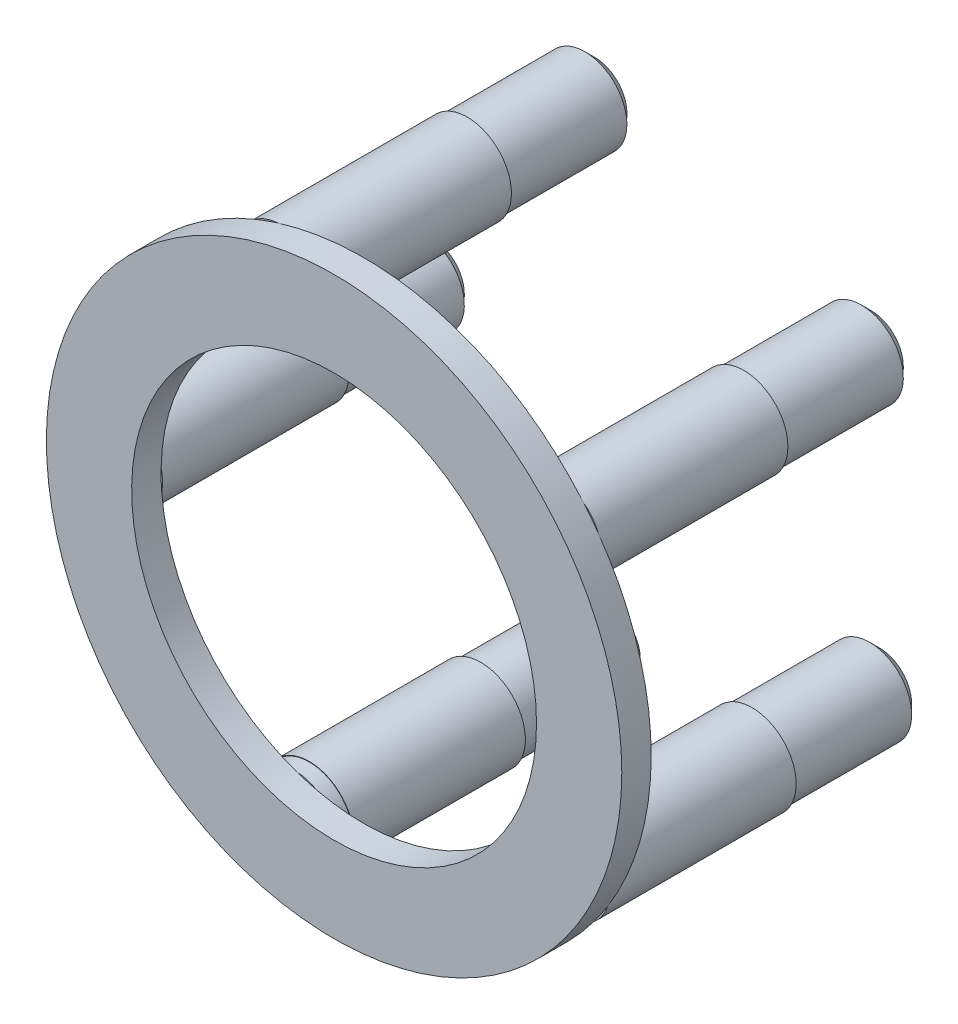
SolidWorks part; units mm, degrees
ref_plane "Front Plane" through (0, 0, 0) normal (0, 0, 1) x (1, 0, 0)
ref_plane "Top Plane" through (0, 0, 0) normal (0, 1, 0) x (1, 0, 0)
ref_plane "Right Plane" through (0, 0, 0) normal (1, 0, 0) x (0, 0, -1)
sketch "Sketch2" plane through (0, 0, -6.0136) normal (0, 0, -1) x (-1, 0, 0)
  circle A0 centre (-20.1422, -37.1244) radius 25 construction
  circle A1 centre (-11.7347, -13.5805) radius 4.5
  circle A2 centre (4.8475, -37.8449) radius 4.5
  circle A3 centre (-13.1052, -61.1136) radius 4.5
  circle A4 centre (-40.7827, -51.2301) radius 4.5
  circle A5 centre (-39.9357, -21.853) radius 4.5
  dimension "D1" = 50
  dimension "D2" = 9
  dimension "D3" = 5
extrude "Boss-Extrude1" add sketch "Sketch2" along normal offset from surface (30 mm away) 11
sketch "Sketch3" plane through (0, 0, -6.0136) normal (0, 0, 1) x (1, 0, 0)
  circle A0 centre (20.1422, -37.1244) radius 29.35
  circle A1 centre (20.1422, -37.1244) radius 20.65
extrude "Boss-Extrude2" add sketch "Sketch3" along normal blind 3
sketch "Sketch4" plane through (0, 0, -36.0136) normal (0, 0, -1) x (-1, 0, 0)
  circle A0 centre (4.8475, -37.8449) radius 4.5
  circle A1 centre (-11.7347, -13.5805) radius 4.5
  circle A2 centre (-39.9357, -21.853) radius 4.5
  circle A3 centre (-40.7827, -51.2301) radius 4.5
  circle A4 centre (-13.1052, -61.1136) radius 4.5
  circle A5 centre (-40.7827, -51.2301) radius 4.5 construction
extrude "Boss-Extrude3" add sketch "Sketch4" along normal blind 2
sketch "Sketch5" plane through (0, 0, -38.0136) normal (0, 0, -1) x (-1, 0, 0)
  circle A0 centre (-13.1052, -61.1136) radius 4.275
  circle A1 centre (-13.1052, -61.1136) radius 4.5
  circle A2 centre (-40.7827, -51.2301) radius 4.275
  circle A3 centre (-40.7827, -51.2301) radius 4.5
  circle A4 centre (-39.9357, -21.853) radius 4.275
  circle A5 centre (-39.9357, -21.853) radius 4.5
  circle A6 centre (-11.7347, -13.5805) radius 4.275
  circle A7 centre (-11.7347, -13.5805) radius 4.5
  circle A8 centre (4.8475, -37.8449) radius 4.275
  circle A9 centre (4.8475, -37.8449) radius 4.5
  point P19 (-20.1422, -37.1244)
  dimension "D1" = 8.55
  dimension "D3" = 9
  dimension "D2" = 5
extrude "Cut-Extrude1" cut sketch "Sketch5" against normal offset from surface (13 mm away) 19 up to face at (26.8675, -14.1977, -6.0136)
chamfer "Chamfer1" distance 1 angle 45 5 edges at (40.7827, -46.9551, -38.0136) (13.1052, -56.8386, -38.0136) (-4.8475, -33.5699, -38.0136) (11.7347, -9.3055, -38.0136) (39.9357, -17.578, -38.0136)
sketch "Sketch6" plane through (0, 0, -25.0136) normal (0, 0, -1) x (-1, 0, 0)
  circle A0 centre (-13.1052, -61.1136) radius 4.55
  dimension "D1" = 9.1
extrude "Boss-Extrude4" add sketch "Sketch6" against normal offset from surface (17.5 mm away) 1.5 up to face at (1.2253, -51.7195, -6.0136)
